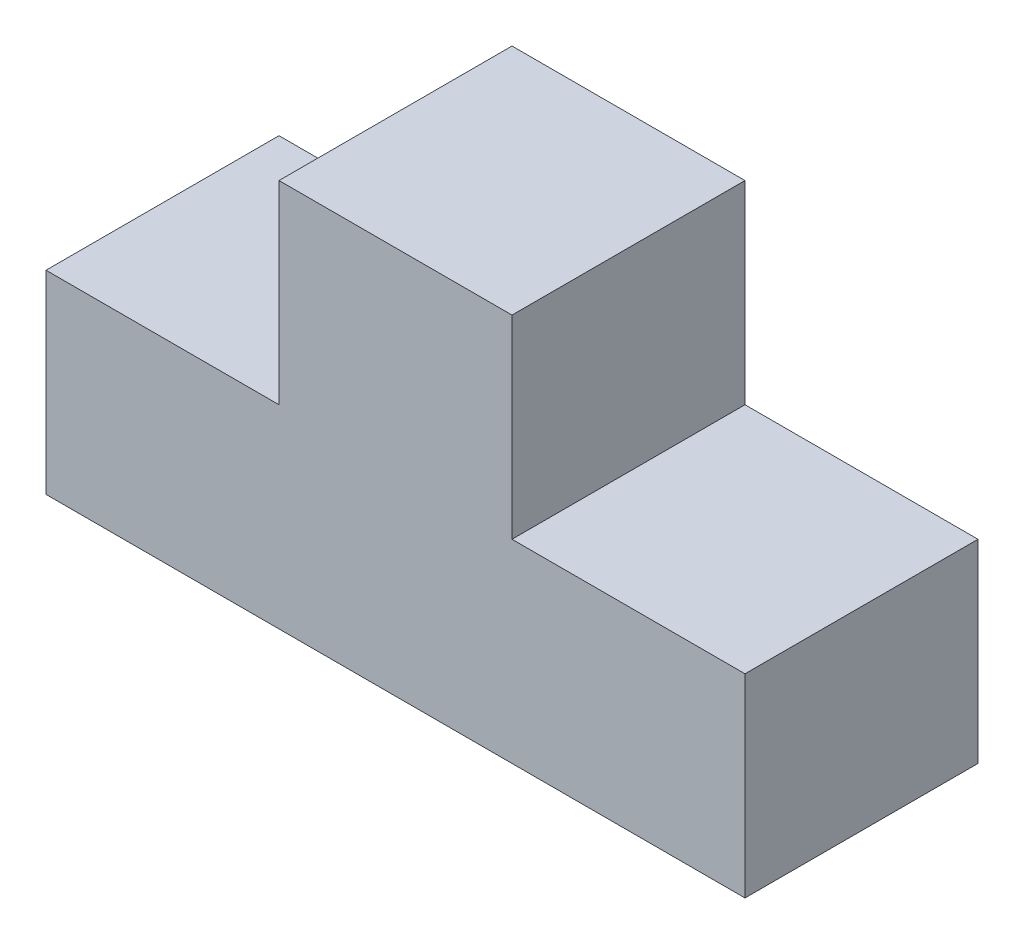
SolidWorks part; units mm, degrees
ref_plane "Front Plane" through (0, 0, 0) normal (0, 0, 1) x (1, 0, 0)
ref_plane "Top Plane" through (0, 0, 0) normal (0, 1, 0) x (1, 0, 0)
ref_plane "Right Plane" through (0, 0, 0) normal (1, 0, 0) x (0, 0, -1)
sketch "Sketch1" plane through (0, 0, 0) normal (0, 0, 1) x (1, 0, 0)
  line L0 (-45, 0) -> (45, 0)
  line L1 (45, 0) -> (45, 25)
  line L2 (45, 25) -> (15, 25)
  line L3 (15, 25) -> (15, 50)
  line L4 (15, 50) -> (-15, 50)
  line L5 (0, 0) -> (0, 50) construction
  line L6 (-45, 0) -> (-45, 25)
  line L7 (-45, 25) -> (-15, 25)
  line L8 (-15, 25) -> (-15, 50)
  dimension "D1" = 90
  dimension "D2" = 30
  dimension "D3" = 25
  dimension "D4" = 25
extrude "Boss-Extrude1" add sketch "Sketch1" along normal blind 30 contours L3 L4 L8 L7 L6 L0 L1 L2
